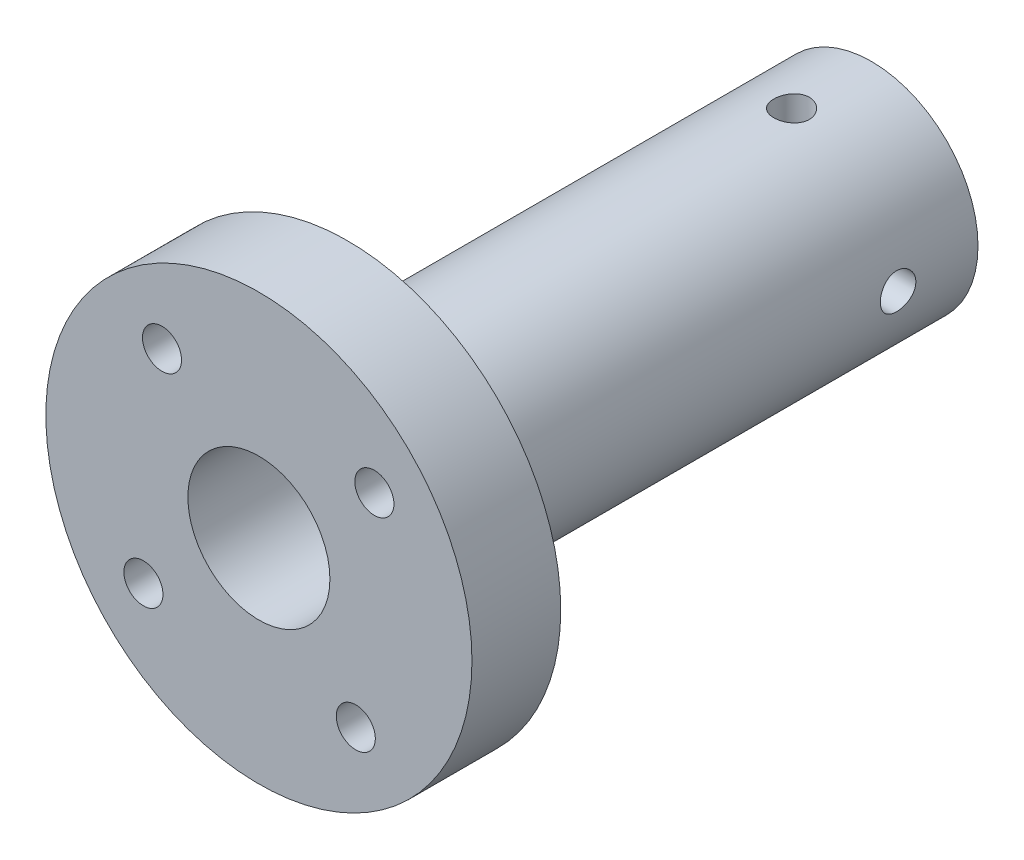
SolidWorks part; units mm, degrees
ref_plane "Ebene vorne" through (0, 0, 0) normal (0, 0, 1) x (1, 0, 0)
ref_plane "Ebene oben" through (0, 0, 0) normal (0, 1, 0) x (1, 0, 0)
ref_plane "Ebene rechts" through (0, 0, 0) normal (1, 0, 0) x (0, 0, -1)
sketch "Skizze1" plane through (0, 0, 0) normal (0, 0, 1) x (1, 0, 0)
  circle A1 centre (0, 0) radius 12.5
  dimension "D2" = 25
extrude "Aufsatz-Linear austragen1" add sketch "Skizze1" along normal blind 40
sketch "Skizze2" plane through (0, 0, 0) normal (1, 0, 0) x (0, 0, -1)
  line L0 (-35, -12.5) -> (-35, -6)
  line L1 (-40, -12.5) -> (0, -12.5) construction
  line L2 (-35, -6) -> (-5, -6)
  line L3 (-5, -6) -> (-5, -12.5)
  line L4 (-35, -12.5) -> (-33.9743, -17.5)
  line L5 (-33.9743, -17.5) -> (-5, -12.5)
  line L6 (0, -12.5) -> (0, 12.5) construction
  line L7 (-35, -12.5) -> (-5, -12.5) construction
  line L8 (-8.1553, -12.5) -> (0, -12.5) construction
  line L9 (0, -12.5) -> (0, -2.7012) construction
  point P0 (-40, -12.5)
  point P1 (-40, 12.5)
  point P11 (0, -12.5)
  dimension "D1" = 5
  dimension "D2" = 5
  dimension "D3" = 90
  dimension "D4" = 6.5
  dimension "D5" = 5
sketch "Skizze3" plane through (0, 0, 0) normal (1, 0, 0) x (0, 0, -1)
  line L0 (-40, 12.5) -> (-40, -12.5) construction
  line L1 (-40, 0) -> (0, 0) construction
  point P0 (-40, -12.5)
  point P1 (-40, 12.5)
  point P3 (0, 12.5)
  point P5 (0, -12.5)
  point P7 (-40, 0)
  point P9 (0, 0)
revolve "Schnitt-Rotation3" cut sketch "Skizze2" angle 360 about L1
sketch "Skizze4" plane through (0, 0, 0) normal (0, 0, 1) x (1, 0, 0)
  circle A0 centre (0, 0) radius 12
  circle A1 centre (0, 0) radius 15
  dimension "D1" = 24
  dimension "D2" = 30
extrude "Schnitt-Linear austragen1" cut sketch "Skizze4" along normal blind 20 from offset 30
sketch "Skizze5" plane through (0, 0, 40) normal (0, 0, 1) x (1, 0, 0)
  line L0 (0, -14.9663) -> (0, 15.9993) construction
  line L1 (0, 0) -> (-5.4573, 6.5037) construction
  circle A0 centre (0, 0) radius 12 construction
  circle A2 centre (-5.4573, 6.5037) radius 1.1
  circle A3 centre (6.5037, 5.4573) radius 1.1
  circle A4 centre (5.4573, -6.5037) radius 1.1
  circle A5 centre (-6.5037, -5.4573) radius 1.1
  point P0 (0, 0)
  point P4 (0, 12.5)
  point P5 (0, -12.5)
  point P7 (0, 12)
  point P9 (0, -12)
  point P35 (0, 0)
  dimension "D3" = 2.2
  dimension "D2" = 40
  dimension "D4" = 4
extrude "Schnitt-Linear austragen2" cut sketch "Skizze5" against normal blind 20
sketch "Skizze6" plane through (0, 0, 0) normal (0, 0, -1) x (-1, 0, 0)
  line L0 (-16.5904, 0) -> (16.1056, 0) construction
  line L1 (0, 15.8638) -> (0, -16.2225) construction
  circle A0 centre (-2.25, 0) radius 1
  circle A1 centre (0, 2.25) radius 1
  circle A2 centre (2.25, 0) radius 1
  circle A3 centre (0, -2.25) radius 1
  point P0 (0, 0)
  point P6 (0, 0)
  point P7 (-1.25, 0)
  point P9 (-2.25, 0)
  point P14 (0, 0)
  point P17 (0, 0)
  point P20 (0, 0)
  point P23 (0, 0)
  dimension "D1" = 1.25
  dimension "D2" = 4
  dimension "D3" = 1
extrude "Schnitt-Linear austragen3" cut sketch "Skizze6" against normal blind 10
sketch "Skizze7" plane through (0, 0, 0) normal (1, 0, 0) x (0, 0, -1)
  line L0 (-40, 0) -> (0, 0) construction
  line L1 (-5.0699, 0) -> (-35.075, 0)
  line L2 (-40, 0) -> (-42.3132, 0)
  line L3 (-35, -4) -> (-5, -4)
  line L4 (-35, -12) -> (-35, 12) construction
  line L5 (-5, 6) -> (-5, -6) construction
  line L6 (-5, -4) -> (-5.0699, 0)
  line L8 (-35, -6) -> (-5, -6) construction
  line L9 (-35, -4) -> (-40, -4)
  line L10 (-40, 12) -> (-40, -12) construction
  line L11 (-35.075, 0) -> (-40, 0)
  line L12 (-42.3132, 0) -> (-42.3132, -4)
  line L13 (-42.3132, -4) -> (-40, -4)
  point P0 (-5.0699, 0)
  point P1 (-35.075, 0)
  dimension "D1" = 2
revolve "Schnitt-Rotation4" cut sketch "Skizze7" angle 360 about L1
sketch "Skizze8" plane through (0, 0, 0) normal (1, 0, 0) x (0, 0, -1)
  line L0 (0, 12.5) -> (-5, 12.5) construction
  line L1 (-5.5, -12.5) -> (0, -12.5)
  line L2 (-5.5, -12.5) -> (-5.5, 12.5)
  line L3 (-5.5, 12.5) -> (0, 12.5)
  line L4 (0, -12.5) -> (0, 12.5)
  line L5 (-5, 12.5) -> (-5, -12.5) construction
  point P0 (-5, -12.5)
  point P1 (-5, 12.5)
  point P8 (0, -12.5)
  point P10 (0, 0)
  point P13 (-5, -12.5)
  dimension "D1" = 0.5
extrude "Schnitt-Linear austragen5" cut sketch "Skizze8" against normal through all both and the other way through all
sketch "Skizze9" plane through (0, 0, 0) normal (1, 0, 0) x (0, 0, -1)
  line L0 (-5.5, -6) -> (-5.5, 6) construction
  line L1 (-40, 0) -> (0, 0) construction
  circle A0 centre (-10, 0) radius 1
  point P0 (-5.5, 0)
  dimension "D1" = 2
  dimension "D2" = 10
extrude "Schnitt-Linear austragen6" cut sketch "Skizze9" against normal through all both and the other way through all
sketch "Skizze11" plane through (0, 0, 0) normal (0, 1, 0) x (1, 0, 0)
  line L0 (0, -40) -> (0, 0) construction
  circle A0 centre (0, -10) radius 1
  dimension "D1" = 2
  dimension "D2" = 10
extrude "Schnitt-Linear austragen7" cut sketch "Skizze11" against normal through all both and the other way through all
